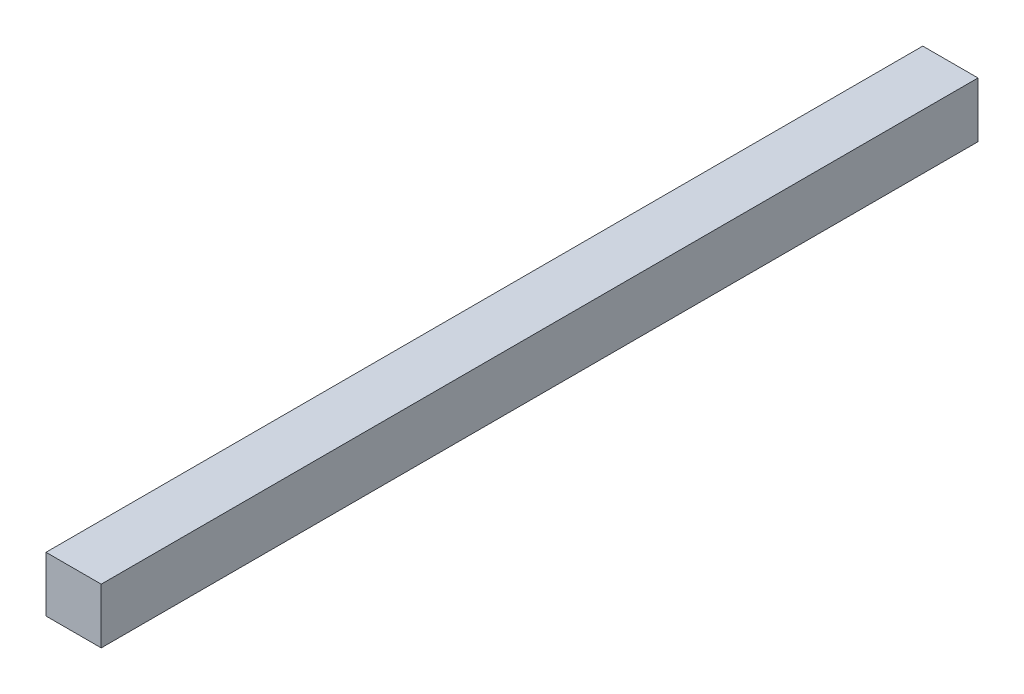
SolidWorks part; units mm, degrees
ref_plane "Front Plane" through (0, 0, 0) normal (0, 0, 1) x (1, 0, 0)
ref_plane "Top Plane" through (0, 0, 0) normal (0, 1, 0) x (1, 0, 0)
ref_plane "Right Plane" through (0, 0, 0) normal (1, 0, 0) x (0, 0, -1)
sketch "Sketch1" plane through (0, 0, 0) normal (0, 0, 1) x (1, 0, 0)
  line L1 (-10.16, -10.16) -> (10.16, -10.16)
  line L2 (-10.16, -10.16) -> (-10.16, 10.16)
  line L3 (-10.16, 10.16) -> (10.16, 10.16)
  line L4 (10.16, -10.16) -> (10.16, 10.16)
  line L5 (-10.16, -10.16) -> (10.16, 10.16) construction
  line L6 (-10.16, 10.16) -> (10.16, -10.16) construction
  point P0 (0, 0)
  dimension "D1" = 20.32
  dimension "D2" = 20.32
extrude "Boss-Extrude1" add sketch "Sketch1" along normal blind 322.58
